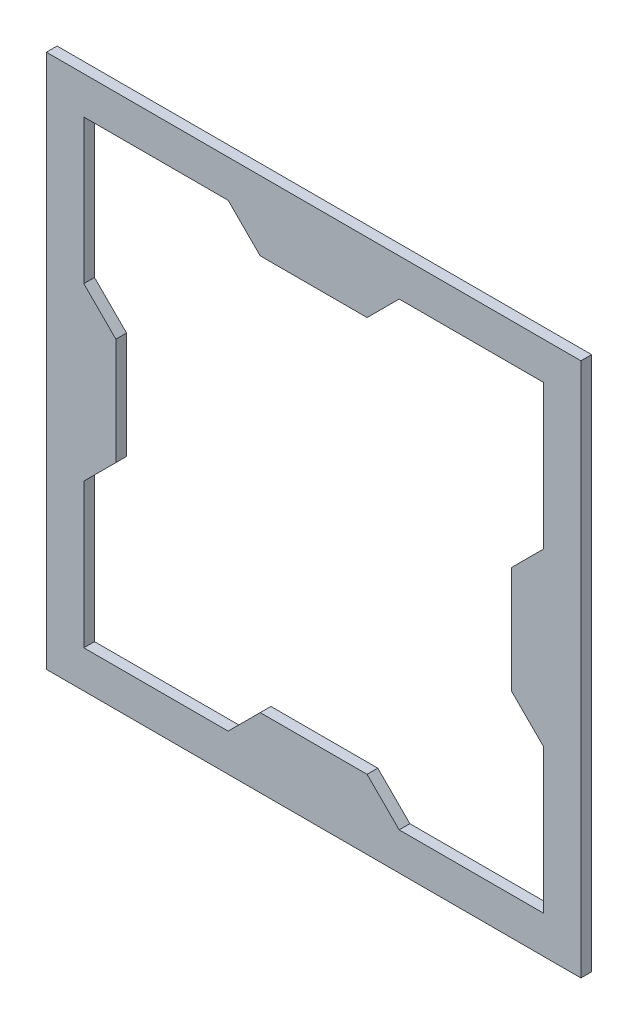
SolidWorks part; units mm, degrees
ref_plane "Front Plane" through (0, 0, 0) normal (0, 0, 1) x (1, 0, 0)
ref_plane "Top Plane" through (0, 0, 0) normal (0, 1, 0) x (1, 0, 0)
ref_plane "Right Plane" through (0, 0, 0) normal (1, 0, 0) x (0, 0, -1)
sketch "Sketch1" plane through (0, 0, 0) normal (0, 0, 1) x (1, 0, 0)
  line L0 (-25.4, 68.2625) -> (-15.875, 58.7375)
  line L1 (79.375, -79.375) -> (-79.375, -79.375)
  line L2 (79.375, -79.375) -> (79.375, 79.375)
  line L3 (79.375, 79.375) -> (-79.375, 79.375)
  line L4 (-79.375, -79.375) -> (-79.375, 79.375)
  line L5 (79.375, -79.375) -> (-79.375, 79.375) construction
  line L6 (79.375, 79.375) -> (-79.375, -79.375) construction
  line L7 (68.2625, -68.2625) -> (-68.2625, -68.2625)
  line L8 (68.2625, -68.2625) -> (68.2625, 68.2625)
  line L9 (68.2625, 68.2625) -> (-68.2625, 68.2625)
  line L10 (-68.2625, -68.2625) -> (-68.2625, 68.2625)
  line L11 (68.2625, -68.2625) -> (-68.2625, 68.2625) construction
  line L12 (68.2625, 68.2625) -> (-68.2625, -68.2625) construction
  line L13 (58.7375, -58.7375) -> (-58.7375, -58.7375)
  line L14 (58.7375, -58.7375) -> (58.7375, 58.7375)
  line L15 (58.7375, 58.7375) -> (-58.7375, 58.7375)
  line L16 (-58.7375, -58.7375) -> (-58.7375, 58.7375)
  line L17 (58.7375, -58.7375) -> (-58.7375, 58.7375) construction
  line L18 (58.7375, 58.7375) -> (-58.7375, -58.7375) construction
  line L19 (15.875, 58.7375) -> (25.4, 68.2625)
  line L20 (68.2625, 25.4) -> (58.7375, 15.875)
  line L21 (58.7375, -15.875) -> (68.2625, -25.4)
  line L22 (25.4, -68.2625) -> (15.875, -58.7375)
  line L23 (-15.875, -58.7375) -> (-25.4, -68.2625)
  line L24 (-68.2625, -25.4) -> (-58.7375, -15.875)
  line L25 (-58.7375, 15.875) -> (-68.2625, 25.4)
  point P0 (0, 0)
  point P6 (0, 0)
  point P11 (0, 0)
  point P35 (0, 0)
  dimension "D1" = 158.75
  dimension "D2" = 158.75
  dimension "D3" = 11.1125
  dimension "D4" = 9.525
  dimension "D5" = 31.75
  dimension "D6" = 15.875
  dimension "D7" = 4
extrude "Boss-Extrude1" add sketch "Sketch1" along normal blind 3.175 contours L4 L1 L2 L3 L7 L10 L9 L8 | L15 L19 L9 L0 | L14 L21 L8 L20 | L13 L23 L7 L22 | L16 L25 L10 L24
